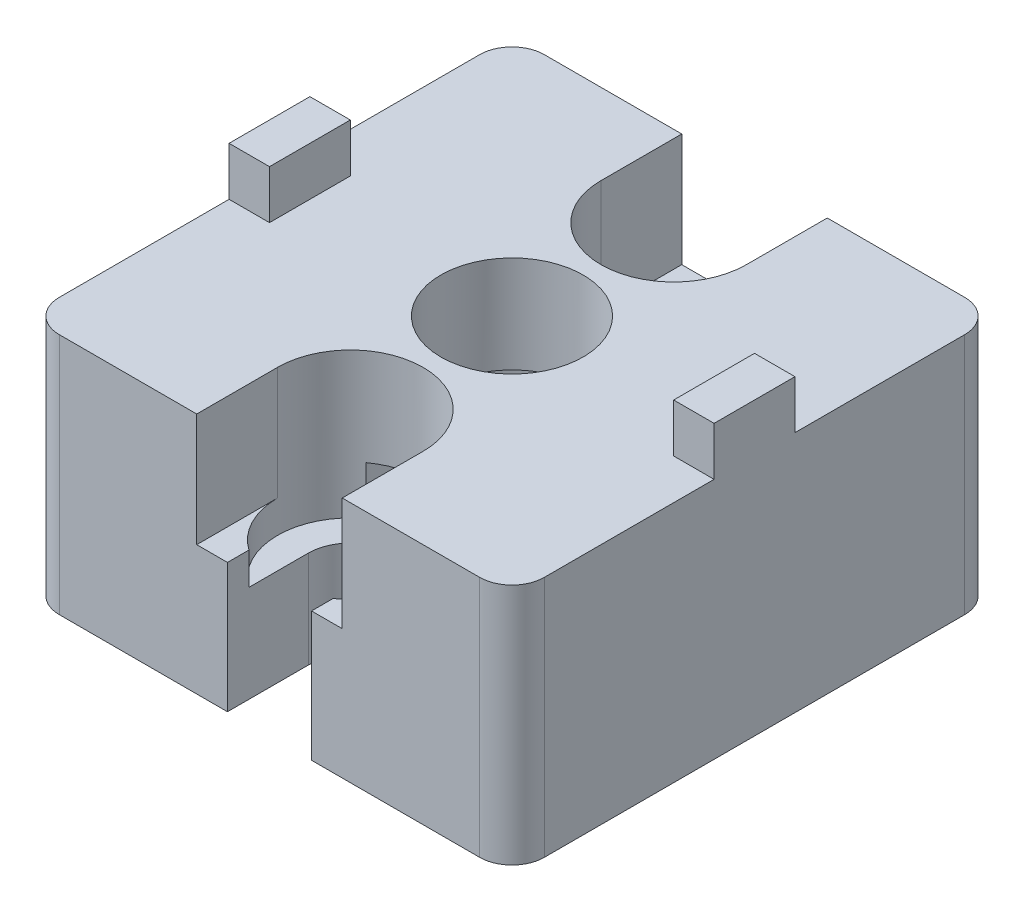
SolidWorks part; units mm, degrees
material "Алюминиевый сплав"
ref_plane "Спереди" through (0, 0, 0) normal (0, 0, 1) x (1, 0, 0)
ref_plane "Сверху" through (0, 0, 0) normal (0, 1, 0) x (1, 0, 0)
ref_plane "Справа" through (0, 0, 0) normal (1, 0, 0) x (0, 0, -1)
sketch "Эскиз1" plane through (0, 0, 0) normal (0, 1, 0) x (1, 0, 0)
  line L1 (15, 15) -> (-15, 15)
  line L2 (15, 15) -> (15, -15)
  line L3 (15, -15) -> (-15, -15)
  line L4 (-15, 15) -> (-15, -15)
  line L5 (15, 15) -> (-15, -15) construction
  line L6 (15, -15) -> (-15, 15) construction
  point P0 (0, 0)
  dimension "D1" = 30
extrude "Бобышка-Вытянуть1" add sketch "Эскиз1" along normal blind 15
sketch "Эскиз2" plane through (0, 15, 0) normal (0, 1, 0) x (1, 0, 0)
  line L0 (-15, 15) -> (-15, -15) construction
  line L1 (-12.5, -2.5) -> (-15, -2.5)
  line L2 (-12.5, -2.5) -> (-12.5, 2.5)
  line L3 (-12.5, 2.5) -> (-15, 2.5)
  line L4 (-15, -2.5) -> (-15, 2.5)
  line L5 (-12.5, -2.5) -> (-15, 2.5) construction
  line L6 (-12.5, 2.5) -> (-15, -2.5) construction
  line L7 (0, 0) -> (0, 6.185) construction
  line L8 (12.5, 2.5) -> (15, -2.5) construction
  line L9 (12.5, -2.5) -> (15, 2.5) construction
  line L10 (15, -2.5) -> (15, 2.5)
  line L11 (12.5, 2.5) -> (15, 2.5)
  line L12 (12.5, -2.5) -> (12.5, 2.5)
  line L13 (12.5, -2.5) -> (15, -2.5)
  point P0 (-13.75, 0)
  point P10 (0, 0)
  point P11 (-15, 1.8997)
  point P16 (13.75, 0)
  dimension "D1" = 2.5
  dimension "D2" = 5
extrude "Бобышка-Вытянуть2" add sketch "Эскиз2" along normal blind 3
sketch "Эскиз3" plane through (0, 15, 0) normal (0, 1, 0) x (1, 0, 0)
  line L0 (-2.6, -15) -> (-2.6, -10)
  line L1 (-15, -15) -> (15, -15) construction
  line L2 (2.6, -10) -> (2.6, -15)
  line L3 (2.6, -15) -> (-2.6, -15)
  line L4 (0, 0) -> (-17.3843, 0) construction
  line L5 (2.6, 10) -> (2.6, 15)
  line L6 (-2.6, 15) -> (-2.6, 10)
  line L7 (2.6, 15) -> (-2.6, 15)
  circle A0 centre (0, 0) radius 4.4
  arc A1 (-2.6, -10) -> (2.6, -10) centre (0, -10) cw
  arc A2 (-2.6, 10) -> (2.6, 10) centre (0, 10) ccw
  point P9 (0, 0)
  dimension "D1" = 8.8
  dimension "D2" = 2.6
  dimension "D3" = 20
extrude "Вырез-Вытянуть1" cut sketch "Эскиз3" against normal through all
sketch "Эскиз4" plane through (0, 0, 0) normal (0, -1, 0) x (1, 0, 0)
  circle A0 centre (0, 0) radius 6.9
  dimension "D1" = 13.8
extrude "Вырез-Вытянуть2" cut sketch "Эскиз4" against normal blind 9
sketch "Эскиз5" plane through (0, 15, 0) normal (0, 1, 0) x (1, 0, 0)
  line L0 (-4.5, -15) -> (-4.5, -10)
  line L1 (-15, -15) -> (-2.6, -15) construction
  line L2 (4.5, -10) -> (4.5, -15)
  line L3 (2.6, -15) -> (15, -15) construction
  line L4 (4.5, -15) -> (-4.5, -15)
  line L5 (0, 0) -> (-17.0309, 0) construction
  line L6 (4.5, 10) -> (4.5, 15)
  line L7 (-4.5, 15) -> (-4.5, 10)
  line L8 (4.5, 15) -> (-4.5, 15)
  arc A0 (-4.5, -10) -> (4.5, -10) centre (0, -10) cw
  arc A3 (-4.5, 10) -> (4.5, 10) centre (0, 10) ccw
  dimension "D1" = 4.5
extrude "Вырез-Вытянуть3" cut sketch "Эскиз5" against normal blind 7
sketch "Эскиз6" plane through (0, 8, 0) normal (0, 1, 0) x (1, 0, 0)
  circle A0 centre (0, -10) radius 4.5
  circle A1 centre (0, 10) radius 4.5
extrude "Вырез-Вытянуть4" cut sketch "Эскиз6" against normal blind 2
fillet "Скругление1" radius 2 4 edges at (-15, 7.5, -15) (15, 7.5, -15) (15, 7.5, 15) (-15, 7.5, 15)
